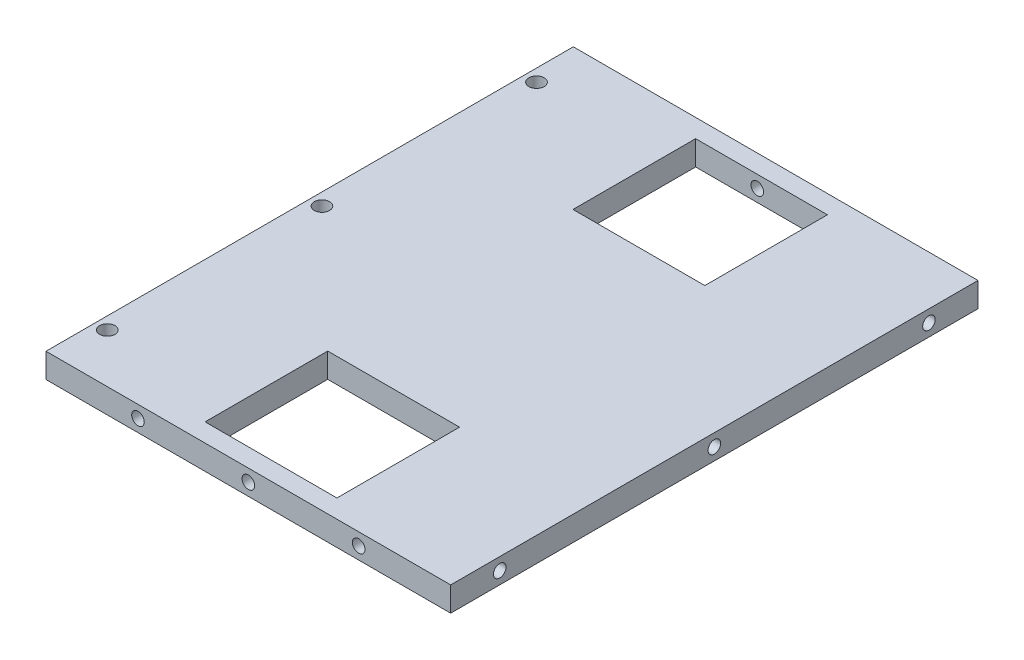
SolidWorks part; units mm, degrees
ref_plane "前视基准面" through (0, 0, 0) normal (0, 0, 1) x (1, 0, 0)
ref_plane "上视基准面" through (0, 0, 0) normal (0, 1, 0) x (1, 0, 0)
ref_plane "右视基准面" through (0, 0, 0) normal (1, 0, 0) x (0, 0, -1)
sketch "草图1" plane through (0, 0, 0) normal (0, 1, 0) x (1, 0, 0)
  line L0 (0, 0) -> (0, 43)
  line L1 (0, 0) -> (0, -43)
  line L2 (66, 43) -> (66, -43)
  line L3 (0, 43) -> (66, 43)
  line L4 (66, -43) -> (0, -43)
  circle A0 centre (2, 0) radius 1.25
  circle A1 centre (2, 35) radius 1.25
  circle A2 centre (2, -35) radius 1.25
  dimension "D1" = 2
  dimension "D2" = 2
extrude "凸台-拉伸1" add sketch "草图1" along normal blind 4
sketch "草图2" plane through (0, 0, 0) normal (0, 1, 0) x (1, 0, 0)
  line L0 (22.9472, -40) -> (44.4472, -40)
  line L1 (44.4472, -20) -> (22.9472, -20)
  line L2 (22.9472, -40) -> (22.9472, -20)
  line L3 (44.4472, -40) -> (44.4472, -20)
  line L4 (0, 0) -> (66, 0) construction
  line L5 (44.4472, 40) -> (44.4472, 20)
  line L6 (22.9472, 40) -> (22.9472, 20)
  line L7 (44.4472, 20) -> (22.9472, 20)
  line L8 (22.9472, 40) -> (44.4472, 40)
extrude "切除-拉伸1" cut sketch "草图2" along normal blind 8
ref_plane "基准面1" through (0, 0, 43) normal (0, 0, 1) x (1, 0, 0)
sketch "草图4" plane through (0, 0, 43) normal (0, 0, 1) x (1, 0, 0)
  line L0 (0, 2) -> (15, 2)
  line L1 (66, 2) -> (51, 2)
  line L3 (33, 0) -> (33, 2)
hole_wizard "M2.5 螺纹孔1" positions "草图5" profile "草图6" tap size "M2.5" standard "GB"
sketch "草图5" plane through (0, 0, 43) normal (0, 0, 1) x (1, 0, 0)
  point P0 (15, 2)
  point P3 (33, 2)
  point P6 (51, 2)
sketch "草图6" plane through (15, 2, 43) normal (1, 0, 0) x (0, -1, 0)
  line L0 (0, 0) -> (0, 8.8659)
  line L1 (0, 8.8659) -> (1.025, 8.25)
  line L2 (1.025, 8.25) -> (1.025, 0)
  line L5 (1.025, 0) -> (0, 0)
  line L10 (0, 8.8659) -> (-1.025, 8.25) construction
  line L11 (0, -6.35) -> (0, 107.95) construction
  dimension "螺纹孔钻头直径" = 2.05
  dimension "螺纹孔钻头深度" = 8.25
  dimension "导头角度" = 118
cosmetic thread "孔螺蚊线1" parameters "D1"=6, "D2"=2.5
cosmetic thread "孔螺蚊线2" parameters "D1"=3, "D2"=2.5
cosmetic thread "孔螺蚊线3" parameters "D1"=6, "D2"=2.5
mirror "镜向1" about plane through (0, 0, 0) normal (0, 0, 1) of "M2.5 螺纹孔1"
ref_plane "基准面2" through (66, 0, 0) normal (1, 0, 0) x (0, 0, -1)
sketch "草图7" plane through (66, 0, 0) normal (1, 0, 0) x (0, 0, -1)
  circle A0 centre (0, 2) radius 1.25
  circle A1 centre (-35, 2) radius 1.25
  circle A2 centre (35, 2) radius 1.25
  dimension "D1" = 2
  dimension "D2" = 2
hole_wizard "M2.5 螺纹孔2" positions "草图8" profile "草图9" tap size "M2.5" standard "GB"
sketch "草图8" plane through (66, 0, 0) normal (1, 0, 0) x (0, 0, -1)
  point P0 (0, 2)
  point P3 (-35, 2)
  point P6 (35, 2)
sketch "草图9" plane through (66, 2, 0) normal (0, 1, 0) x (0, 0, -1)
  line L0 (0, 0) -> (0, 7.8659)
  line L1 (0, 7.8659) -> (1.025, 7.25)
  line L2 (1.025, 7.25) -> (1.025, 0)
  line L5 (1.025, 0) -> (0, 0)
  line L10 (0, 7.8659) -> (-1.025, 7.25) construction
  line L11 (0, -6.35) -> (0, 107.95) construction
  dimension "螺纹孔钻头直径" = 2.05
  dimension "螺纹孔钻头深度" = 7.25
  dimension "导头角度" = 118
cosmetic thread "孔螺蚊线4" parameters "D1"=5, "D2"=2.5
cosmetic thread "孔螺蚊线5" parameters "D1"=5, "D2"=2.5
cosmetic thread "孔螺蚊线6" parameters "D1"=5, "D2"=2.5
